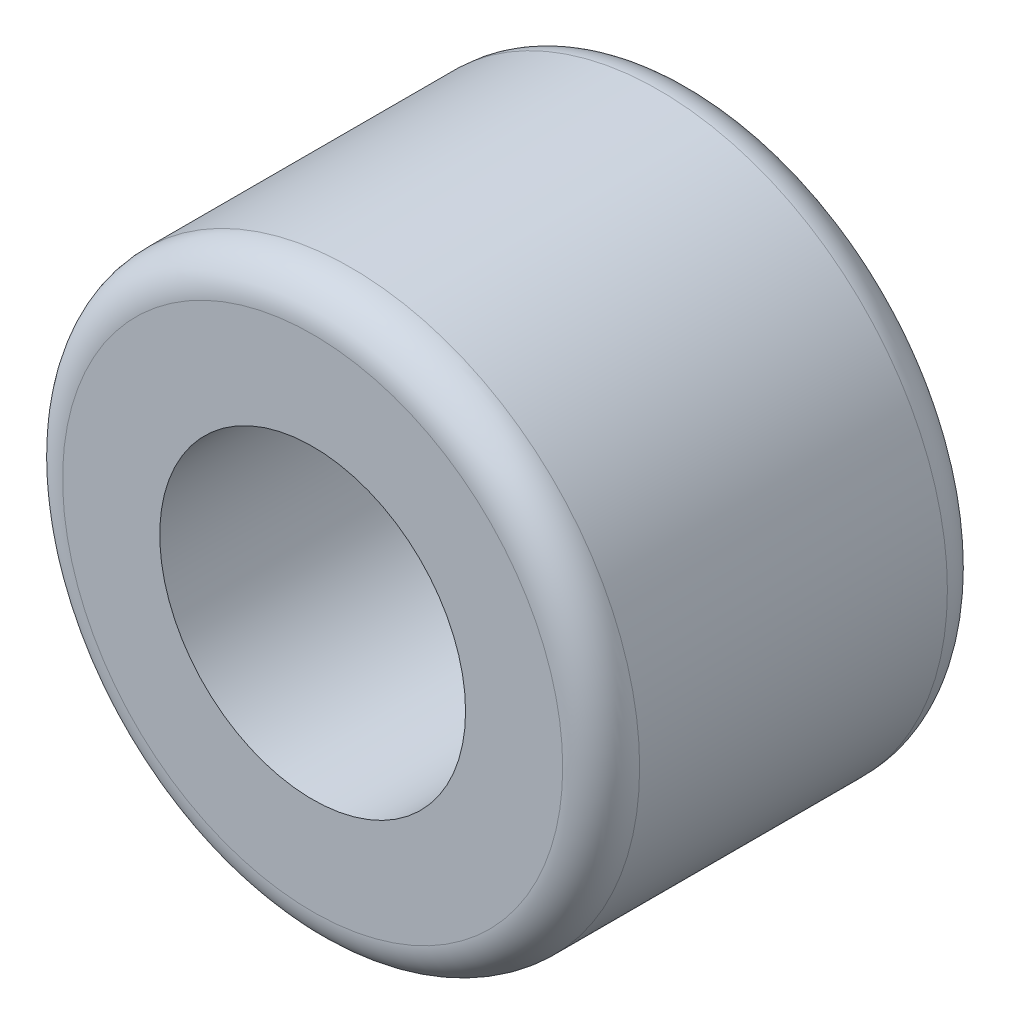
SolidWorks part; units mm, degrees
ref_plane "Alzado" through (0, 0, 0) normal (0, 0, 1) x (1, 0, 0)
ref_plane "Planta" through (0, 0, 0) normal (0, 1, 0) x (1, 0, 0)
ref_plane "Vista lateral" through (0, 0, 0) normal (1, 0, 0) x (0, 0, -1)
sketch "Croquis1" plane through (0, 0, 0) normal (0, 0, 1) x (1, 0, 0)
  circle A0 centre (0, 0) radius 7.5
  circle A1 centre (0, 0) radius 3.975
  dimension "D1" = 15
  dimension "D2" = 7.95
extrude "Saliente-Extruir1" add sketch "Croquis1" along normal mid plane 10
fillet "Redondeo2" radius 1 2 edges at (7.5, 0, 5) (7.5, 0, -5)
